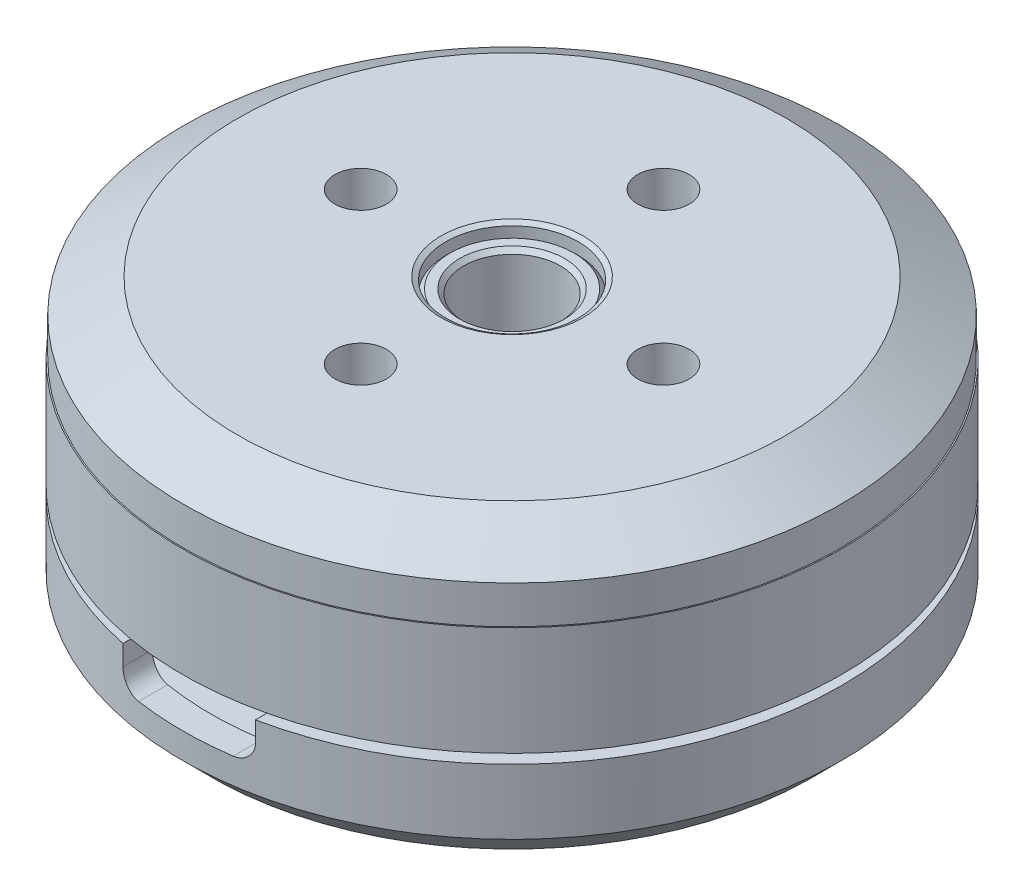
SolidWorks part; units mm, degrees
ref_plane "Front Plane" through (0, 0, 0) normal (0, 0, 1) x (1, 0, 0)
ref_plane "Top Plane" through (0, 0, 0) normal (0, 1, 0) x (1, 0, 0)
ref_plane "Right Plane" through (0, 0, 0) normal (1, 0, 0) x (0, 0, -1)
sketch "Sketch1" plane through (0, 0, 0) normal (1, 0, 0) x (0, 0, -1)
  line L0 (0, 0) -> (0, 81.8982) construction
  line L1 (15.9, 0) -> (3.25, 0)
  line L2 (3.25, 0) -> (3.25, -0.75)
  line L3 (3.25, -0.75) -> (3.5, -0.75)
  line L4 (3.5, -0.75) -> (3.5, -1.2)
  line L5 (3.5, -1.2) -> (3.2, -1.5)
  line L6 (3.2, -1.5) -> (2.55, -1.5)
  line L7 (2.55, -1.5) -> (2.55, 14.175)
  line L8 (2.55, 14.175) -> (2.775, 14.4)
  line L9 (2.775, 14.4) -> (3.275, 14.4)
  line L10 (3.275, 14.4) -> (3.5, 14.175)
  line L11 (3.5, 14.175) -> (3.5, 14.8057)
  line L12 (3.5, 14.8057) -> (3.75, 14.95)
  line L13 (3.75, 14.95) -> (14.5, 14.95)
  line L14 (14.5, 14.95) -> (17.35, 13.2)
  line L15 (17.35, 13.2) -> (17.35, 11.2)
  line L16 (17.35, 11.2) -> (17.415, 11.2)
  line L17 (17.415, 11.2) -> (17.415, 5.45)
  line L18 (17.415, 5.45) -> (16.415, 5.45)
  line L19 (16.415, 5.45) -> (16.415, 11.4272)
  line L20 (16.415, 11.4272) -> (12.5, 13.8311)
  line L21 (12.5, 13.8311) -> (12.5, 4.95)
  line L22 (12.5, 4.95) -> (17.415, 4.95) construction
  line L23 (17.415, 4.95) -> (17.415, 1.515)
  line L24 (17.415, 1.515) -> (15.9, 0)
  line L25 (15.9, 4.95) -> (15.9, 2)
  line L26 (15.9, 2) -> (12.5, 2)
  line L27 (12.5, 2) -> (12.5, 4.95)
  line L28 (15.9, 4.95) -> (17.415, 4.95)
  dimension "D1" = 5.1
  dimension "D2" = 7
  dimension "D3" = 0.5
  dimension "D4" = 45
  dimension "D5" = 7.5
  dimension "D6" = 30
  dimension "D7" = 29
  dimension "D8" = 34.7
  dimension "D9" = 34.83
  dimension "D10" = 31.8
  dimension "D11" = 6.5
  dimension "D12" = 0.75
  dimension "D13" = 45
  dimension "D14" = 1.5
  dimension "D15" = 0.65
  dimension "D16" = 0.55
  dimension "D17" = 1.75
  dimension "D18" = 3.75
  dimension "D19" = 14.95
  dimension "D20" = 4.95
  dimension "D21" = 2
  dimension "D22" = 1
  dimension "D23" = 0.5
  dimension "D24" = 25
  dimension "D25" = 2
revolve "Revolve1" add sketch "Sketch1" angle 360 about L0
sketch "Sketch3" plane through (0, 0, 0) normal (1, 0, 0) x (0, 0, -1)
  line L0 (0, 0) -> (0, 4.3921) construction
  line L1 (5.5, 0) -> (5.5, -0.6257)
  line L2 (-15.9, 0) -> (15.9, 0) construction
  line L3 (5.5, 0) -> (5.5, 0.0404)
  line L4 (5.5, 0.0404) -> (5.4646, 0.005)
  line L5 (5.4646, 0.005) -> (5.0354, 0.005)
  line L6 (5.0354, 0.005) -> (5, 0.0404)
  line L7 (5, 0.0404) -> (5, 0.065)
  line L8 (5, 0.065) -> (3.75, 0.065)
  line L9 (3.75, 0.065) -> (3.75, 0.0404)
  line L10 (3.75, 0.0404) -> (3.7146, 0.005)
  line L11 (3.7146, 0.005) -> (3.2854, 0.005)
  line L12 (3.2854, 0.005) -> (3.25, 0.0404)
  line L13 (3.25, 0.0404) -> (3.25, -0.0717)
  line L14 (3.25, -0.0717) -> (5.5, -0.6257)
  dimension "D1" = 11
  dimension "D2" = 6.5
  dimension "D3" = 0.005
  dimension "D4" = 0.05
  dimension "D5" = 45
  dimension "D6" = 0.5
  dimension "D7" = 0.5
  dimension "D8" = 0.06
revolve "Cut-Revolve1" cut sketch "Sketch3" angle 360 about L0
sketch "Sketch4" plane through (0, 14.95, 0) normal (0, 1, 0) x (1, 0, 0)
  line L0 (0, 0) -> (0, 8) construction
  circle A0 centre (0, 8) radius 1.36
  circle A1 centre (8, 0) radius 1.36
  circle A2 centre (0, -8) radius 1.36
  circle A3 centre (-8, 0) radius 1.36
  point P13 (0, 0)
  dimension "D1" = 8
  dimension "D2" = 2.72
  dimension "D3" = 4
extrude "Cut-Extrude1" cut sketch "Sketch4" against normal blind 4
sketch "Sketch5" plane through (0, 0, 0) normal (0, -1, 0) x (1, 0, 0)
  line L0 (0, 0) -> (0, 8) construction
  line L1 (0, 0) -> (9.5, 0) construction
  line L2 (0, 0) -> (5.6569, -5.6569) construction
  line L3 (0, 0) -> (-6.7175, -6.7175) construction
  circle A0 centre (0, 0) radius 8 construction
  circle A1 centre (0, 0) radius 9.5 construction
  circle A2 centre (-6.7175, -6.7175) radius 1.36
  circle A3 centre (5.6569, -5.6569) radius 1.36
  circle A4 centre (-5.6569, 5.6569) radius 1.36
  circle A5 centre (6.7175, 6.7175) radius 1.36
  dimension "D3" = 45
  dimension "D4" = 2.72
  dimension "D1" = 8
  dimension "D2" = 19
extrude "Cut-Extrude2" cut sketch "Sketch5" against normal blind 4
sketch "Sketch6" plane through (0, 0, 0) normal (1, 0, 0) x (0, 0, -1)
  line L1 (-12.5, 5.1707) -> (-18.2264, 5.1707)
  line L2 (-12.5, 5.1707) -> (-12.5, 2.8801)
  line L3 (-12.5, 2.8801) -> (-18.2264, 2.8801)
  line L4 (-18.2264, 5.1707) -> (-18.2264, 2.8801)
  dimension "D1" = 12.5
extrude "Cut-Extrude3" cut sketch "Sketch6" against normal mid plane 7
fillet "Fillet1" radius 1 2 edges at (-3.5, 2.8801, 16.2848) (3.5, 2.8801, 16.2848)
